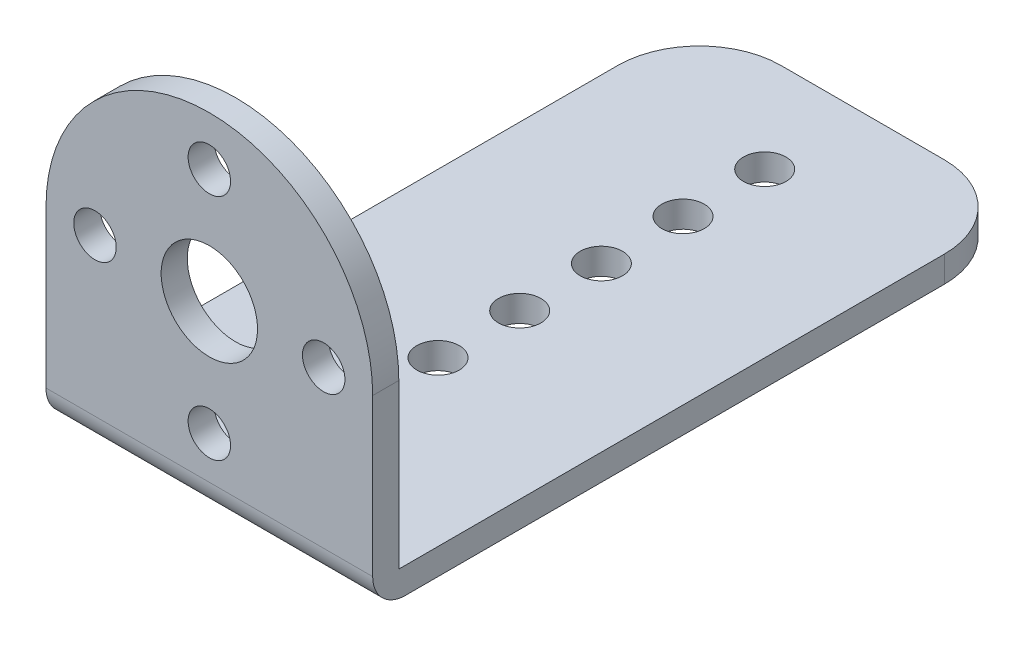
SolidWorks part; units mm, degrees
ref_plane "Front Plane" through (0, 0, 0) normal (0, 0, 1) x (1, 0, 0)
ref_plane "Top Plane" through (0, 0, 0) normal (0, 1, 0) x (1, 0, 0)
ref_plane "Right Plane" through (0, 0, 0) normal (1, 0, 0) x (0, 0, -1)
sketch "Sketch1" plane through (0, 0, 0) normal (0, 0, 1) x (1, 0, 0)
  line L0 (-20.6689, 0) -> (27.0286, 0) construction
  line L1 (-12.7, 0) -> (-12.7, -14.732)
  line L2 (12.7, 0) -> (12.7, -14.732)
  line L3 (-12.7, -14.732) -> (12.7, -14.732)
  arc A0 (12.7, 0) -> (-12.7, 0) centre (0, 0) ccw
  circle A1 centre (0, 0) radius 3.7465
  circle A2 centre (0, 8.89) radius 1.651
  circle A3 centre (8.89, 0) radius 1.651
  circle A4 centre (0, -8.89) radius 1.651
  circle A5 centre (-8.89, 0) radius 1.651
  point P20 (0, 0)
  dimension "D1" = 25.4
  dimension "D3" = 7.493
  dimension "D4" = 3.302
  dimension "D2" = 14.732
  dimension "D5" = 8.89
  dimension "D6" = 4
extrude "Boss-Extrude1" add sketch "Sketch1" against normal blind 2.032
sketch "Sketch2" plane through (0, -14.732, 0) normal (0, -1, 0) x (1, 0, 0)
  line L1 (-12.7, 0) -> (12.7, 0)
  line L2 (-12.7, 0) -> (-12.7, -50.8)
  line L3 (-12.7, -50.8) -> (12.7, -50.8)
  line L4 (12.7, 0) -> (12.7, -50.8)
  circle A0 centre (0, -43.18) radius 1.651
  circle A1 centre (0, -36.83) radius 1.651
  circle A2 centre (0, -30.48) radius 1.651
  circle A3 centre (0, -24.13) radius 1.651
  circle A4 centre (0, -17.78) radius 1.651
  circle A5 centre (0, -11.43) radius 1.651
  circle A6 centre (0, -5.08) radius 1.651
  dimension "D3" = 3.302
  dimension "D6" = 3.302
  dimension "D1" = 25.4
  dimension "D2" = 50.8
  dimension "D4" = 7.62
  dimension "D5" = 6.35
  dimension "D7" = 6
extrude "Boss-Extrude3" add sketch "Sketch2" against normal blind 2.032
fillet "Fillet3" radius 2.54 1 edges at (0, -14.732, 0)
fillet "Fillet4" radius 6.35 2 edges at (12.7, -13.716, -50.8) (-12.7, -13.716, -50.8)
